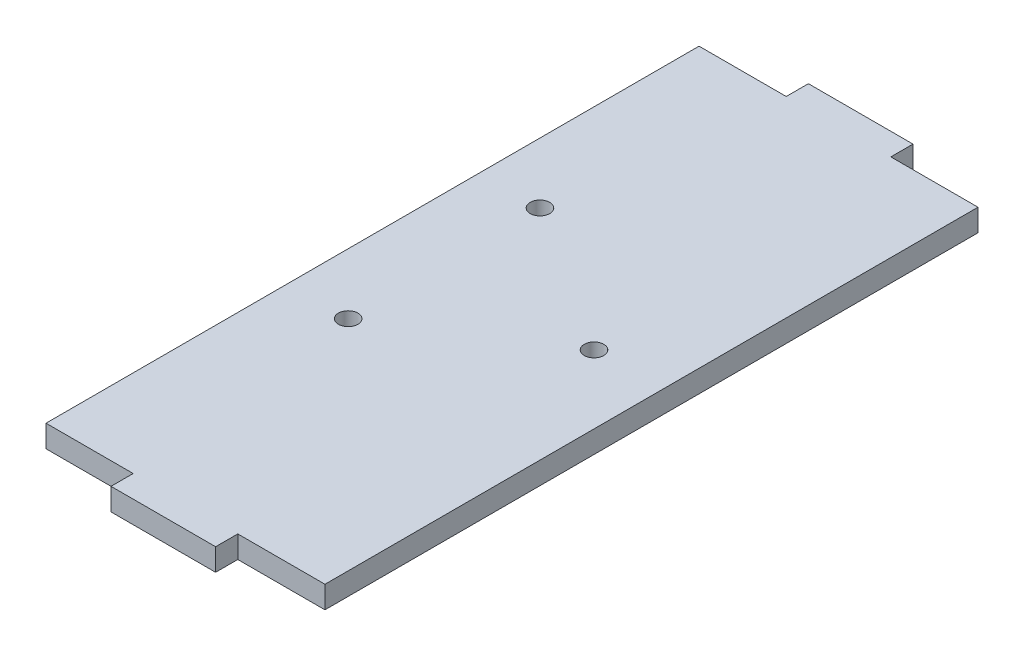
SolidWorks part; units mm, degrees
ref_plane "Front Plane" through (0, 0, 0) normal (0, 0, 1) x (1, 0, 0)
ref_plane "Top Plane" through (0, 0, 0) normal (0, 1, 0) x (1, 0, 0)
ref_plane "Right Plane" through (0, 0, 0) normal (1, 0, 0) x (0, 0, -1)
sketch "Sketch1" plane through (0, 0, 0) normal (0, 1, 0) x (1, 0, 0)
  line L1 (20, -50) -> (-20, -50)
  line L2 (20, -50) -> (20, 50)
  line L3 (20, 50) -> (-20, 50)
  line L4 (-20, -50) -> (-20, 50)
  line L5 (20, -50) -> (-20, 50) construction
  line L6 (20, 50) -> (-20, -50) construction
  point P0 (0, 0)
  dimension "D1" = 40
  dimension "D2" = 100
extrude "Boss-Extrude1" add sketch "Sketch1" along normal blind 3.18
sketch "Sketch2" plane through (0, 3.18, 0) normal (0, 1, 0) x (1, 0, 0)
  line L0 (20, 50) -> (-20, 50) construction
  line L1 (7.5, 50) -> (20, 50)
  line L2 (7.5, 50) -> (7.5, 46.82)
  line L3 (7.5, 46.82) -> (20, 46.82)
  line L4 (20, 50) -> (20, 46.82)
  line L5 (20, -50) -> (20, 50) construction
  line L6 (-20, 50) -> (-20, -50) construction
  line L7 (-7.5, 50) -> (-20, 50)
  line L8 (-7.5, 50) -> (-7.5, 46.82)
  line L9 (-7.5, 46.82) -> (-20, 46.82)
  line L10 (-20, 50) -> (-20, 46.82)
  dimension "D1" = 3.18
  dimension "D2" = 3.18
  dimension "D3" = 15
  dimension "D4" = 12.5
  dimension "D5" = 12.5
extrude "Cut-Extrude1" cut sketch "Sketch2" against normal through all
mirror "Mirror1" about plane through (0, 0, 0) normal (0, 0, 1) of "Cut-Extrude1"
sketch "Sketch3" plane through (0, 3.18, 0) normal (0, 1, 0) x (1, 0, 0)
  circle A0 centre (-11.3096, -12.1802) radius 1.4 construction
  circle A1 centre (10.1904, 1.5698) radius 1.4 construction
  circle A2 centre (-11.3096, 15.3198) radius 1.4 construction
  circle A3 centre (-11.3096, -12.1802) radius 1.4
  circle A4 centre (10.1904, 1.5698) radius 1.4
  circle A5 centre (-11.3096, 15.3198) radius 1.4
extrude "Cut-Extrude2" cut sketch "Sketch3" against normal through all
